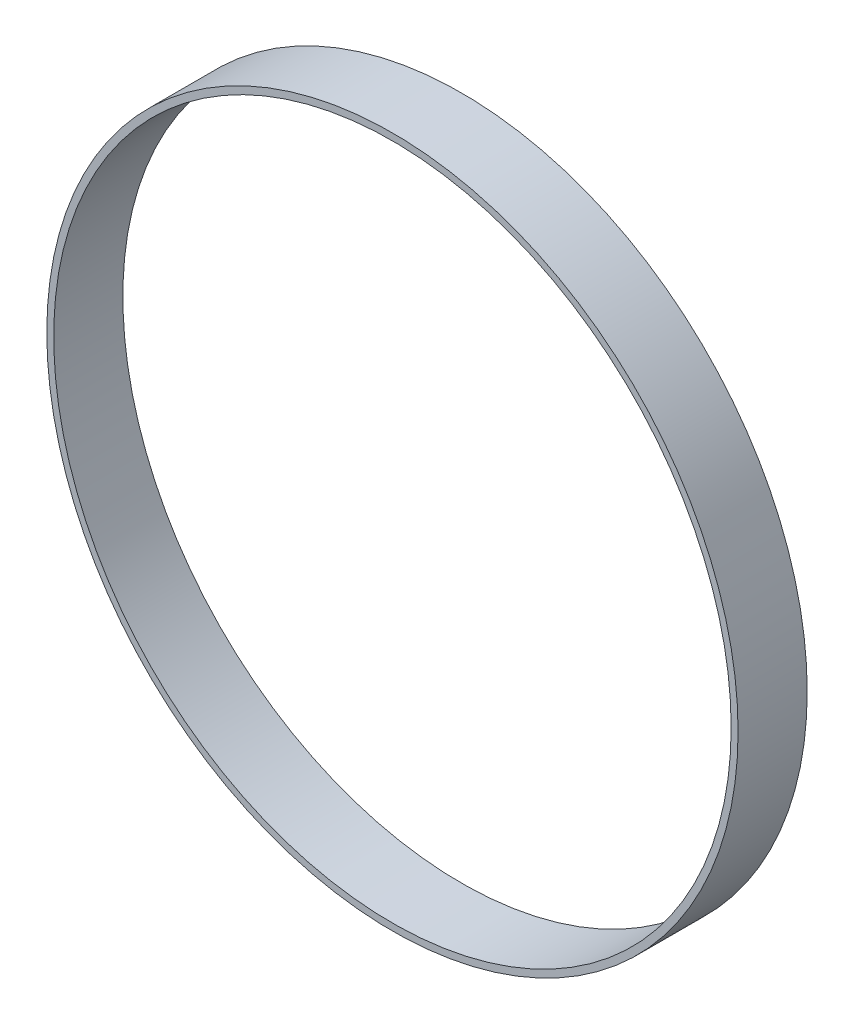
SolidWorks part; units mm, degrees
ref_plane "Front Plane" through (0, 0, 0) normal (0, 0, 1) x (1, 0, 0)
ref_plane "Top Plane" through (0, 0, 0) normal (0, 1, 0) x (1, 0, 0)
ref_plane "Right Plane" through (0, 0, 0) normal (1, 0, 0) x (0, 0, -1)
sketch "Sketch1" plane through (0, 0, 0) normal (0, 0, 1) x (1, 0, 0)
  circle A0 centre (0, 0) radius 98
  circle A1 centre (0, 0) radius 100
  dimension "D1" = 196
  dimension "D2" = 200
extrude "Boss-Extrude1" add sketch "Sketch1" along normal blind 20
